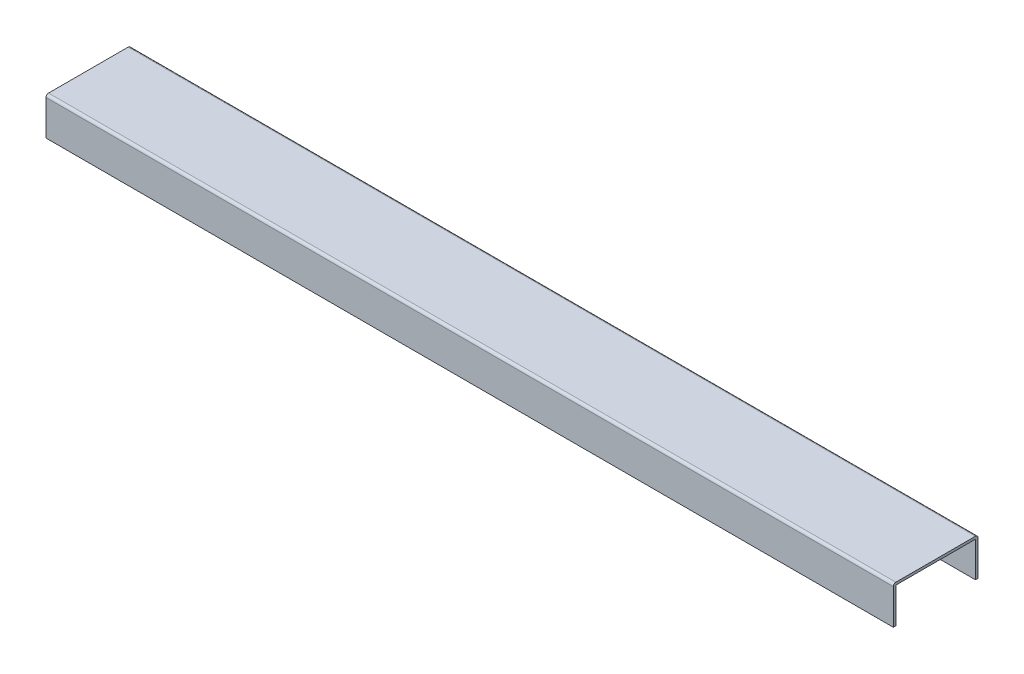
SolidWorks part; units mm, degrees
ref_plane "Спереди" through (0, 0, 0) normal (0, 0, 1) x (1, 0, 0)
ref_plane "Сверху" through (0, 0, 0) normal (0, 1, 0) x (1, 0, 0)
ref_plane "Справа" through (0, 0, 0) normal (1, 0, 0) x (0, 0, -1)
sketch "Эскиз1" plane through (0, 0, 0) normal (1, 0, 0) x (0, 0, -1)
  line L1 (3, 0) -> (97, 0)
  line L2 (0, 3) -> (0, 97)
  line L3 (3, 100) -> (97, 100)
  line L4 (100, 3) -> (100, 97)
  arc A0 (0, 3) -> (3, 0) centre (3, 3) ccw
  arc A1 (97, 0) -> (100, 3) centre (97, 3) ccw
  arc A2 (97, 100) -> (100, 97) centre (97, 97) cw
  arc A3 (0, 97) -> (3, 100) centre (3, 97) cw
  point P7 (0, 0)
  dimension "D1" = 3
extrude "Вытянуть-Тонкостенный1" add sketch "Эскиз1" along normal blind 1000 thin
sketch "Эскиз2" plane through (0, 0, -100) normal (0, 0, -1) x (-1, 0, 0)
  line L0 (0, 3) -> (0, 97) construction
  line L1 (-1000, 0) -> (0, 0)
  line L2 (-1000, 0) -> (-1000, 55.462)
  line L3 (-1000, 55.462) -> (0, 55.462)
  line L4 (0, 0) -> (0, 55.462)
extrude "Вырез-Вытянуть1" cut sketch "Эскиз2" against normal through all
